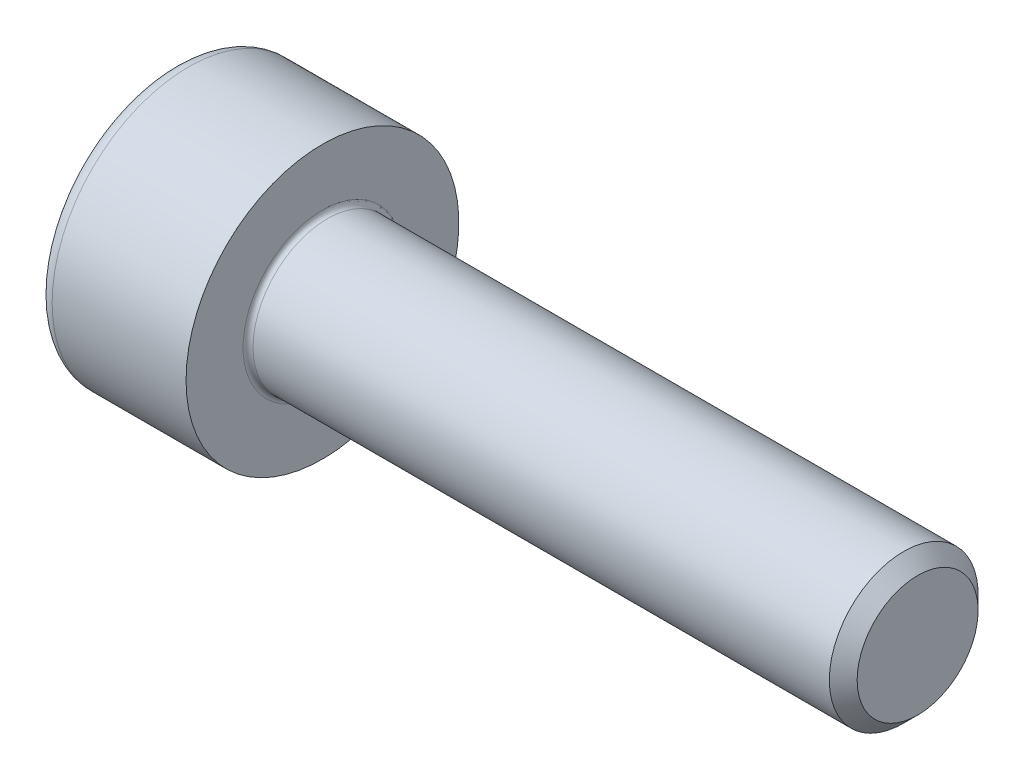
SolidWorks part; units mm, degrees
revolve "Base-Revolve" add sketch "BodySke"
sketch "BodySke" plane through (0, 0, 0) normal (0, 0, 1) x (1, 0, 0)
  line L0 (0, 0) -> (0, 2.75)
  line L1 (0, 2.75) -> (3, 2.75)
  line L2 (3, 2.75) -> (3, 1.5)
  line L3 (3, 1.5) -> (14.7195, 1.5)
  line L4 (15, 1.2195) -> (15, 0)
  line L5 (15, 0) -> (0, 0)
  line L6 (-31.75, 0) -> (127, 0) construction
  line L8 (15, 1.2195) -> (14.7195, 1.5)
  line L10 (15, -1.2195) -> (14.7195, -1.5) construction
  line L11 (3.5, 9.525) -> (3.5, 3.175) construction
  line L12 (3, 9.525) -> (3, 3.175) construction
  line L13 (-45, 9.525) -> (-45, 3.175) construction
  dimension "Head_ht" = 3
  dimension "Length" = 12
  dimension "Body_ch_ang" = 45
  dimension "Diameter" = 3
  dimension "Minor_dia" = 2.439
  dimension "Advance" = 0.5
  dimension "Thread_nom" = 12
  dimension "Thread_length" = 60
  dimension "Head_dia" = 5.5
cosmetic thread "ThreadCosmetic" [suppressed]
fillet "Fillet1" radius 0.1 1 edges at (3, 0, 1.5)
fillet "Fillet2" radius 0.3 1 edges at (0, 0, 2.75)
ref_plane "Plane1" through (0, 0, 0) normal (0, 0, 1) x (1, 0, 0)
ref_plane "Plane2" through (0, 0, 0) normal (0, 1, 0) x (1, 0, 0)
ref_plane "Plane3" through (0, 0, 0) normal (1, 0, 0) x (0, 0, -1)
sketch "Sketch2" plane through (0, 0, 0) normal (0, 0, 1) x (1, 0, 0)
  line L0 (0, 1.26) -> (1.3, 1.26)
  line L1 (1.3, 1.26) -> (2.0275, 0)
  line L2 (-31.75, 0) -> (127, 0) construction
  line L3 (2.0275, 0) -> (0, 0)
  line L4 (0, 0) -> (0, 1.26)
  line L6 (0, 0) -> (47.625, 0) construction
  dimension "D1" = 1.26
  dimension "D2" = 60
  dimension "Depth" = 1.3
revolve "Hex-PreBroach" cut sketch "Sketch2" angle 360 about L6
sketch "Sketch3" plane through (0, 0, 0) normal (-1, 0, 0) x (0, 0.5, 0.866)
  line L0 (0.7275, 1.26) -> (-0.7275, 1.26)
  line L1 (-0.7275, 1.26) -> (-1.4549, 0)
  line L2 (0.7275, 1.26) -> (1.4549, 0)
  line L3 (0.7275, -1.26) -> (1.4549, 0)
  line L4 (0.7275, -1.26) -> (-0.7275, -1.26)
  line L5 (-0.7275, -1.26) -> (-1.4549, 0)
  dimension "D1" = 1.26
  dimension "D2" = 1.26
  dimension "Hex_size" = 2.52
extrude "Hex" cut sketch "Sketch3" against normal blind 1.3
sketch "ThdSchSke" plane through (0, 0, 0) normal (0, 0, 1) x (1, 0, 0)
  line L0 (4.5, -1.2195) -> (4.3036, -1.5)
  line L1 (4.5, -1.2195) -> (4.6964, -1.5)
  line L2 (4.6964, -1.5) -> (4.6964, -1.875)
  line L3 (-3.175, 0) -> (5.1513, 0) construction
  line L4 (0, 2.45) -> (0, -2.45) construction
  line L5 (4.6964, -1.875) -> (4.3036, -1.875)
  line L6 (4.3036, -1.875) -> (4.3036, -1.5)
  dimension "Thread_minor" = 2.439
  dimension "Diameter" = 3
  dimension "Start" = 4.5
revolve "ThreadSchematic" [suppressed] cut sketch "ThdSchSke" angle 360 about L3
pattern_linear "ThdSchPat" [suppressed]
equation "\"D2@Sketch3\" = \"Hex_size@Sketch3\" / 2"
equation "\"D1@Sketch3\" = \"Hex_size@Sketch3\" / 2"
equation "\"D1@Sketch2\" = \"Hex_size@Sketch3\" / 2"
equation "\"Thread_minor@ThreadCosmetic\"  =  \"Minor_dia@BodySke\""
equation "\"Depth@Sketch2\" =  \"Key_eng@Hex\""
equation "\"Thread_length@ThreadCosmetic\" = ((sgn( (\"Length@BodySke\" - \"Advance@BodySke\" * 3.0) - \"Thread_nom@BodySke\" )-1)*( (\"Length@BodySke\" - \"Advance@BodySke\" * 3.0) - \"Thread_nom@BodySke\" ))/-2+ \"Thread_nom@BodySke\""
equation "\"Thread_minor@ThdSchSke\" = \"Minor_dia@BodySke\""
equation "\"Diameter@ThdSchSke\" = \"Diameter@BodySke\""
equation "\"Overcut@ThdSchSke\" = \"Diameter@BodySke\" * 1.25"
equation "\"Start@ThdSchSke\" = \"Head_ht@BodySke\" + \"Length@BodySke\" - \"Thread_length@ThreadCosmetic\"  '---Non-countersunk---"
equation "\"Num_threads@ThdSchPat\" = int( \"Thread_length@ThreadCosmetic\" / \"Advance@BodySke\" + 0.999 )  + 1"
equation "\"Advance@ThdSchPat\" = \"Thread_length@ThreadCosmetic\" /  (\"Num_threads@ThdSchPat\" - 1) 'relax it"
equation "\"Num_threads@ThdSchPat\" = \"Num_threads@ThdSchPat\" - sgn( \"Num_threads@ThdSchPat\" - 1) '---chamfered tips only---"
